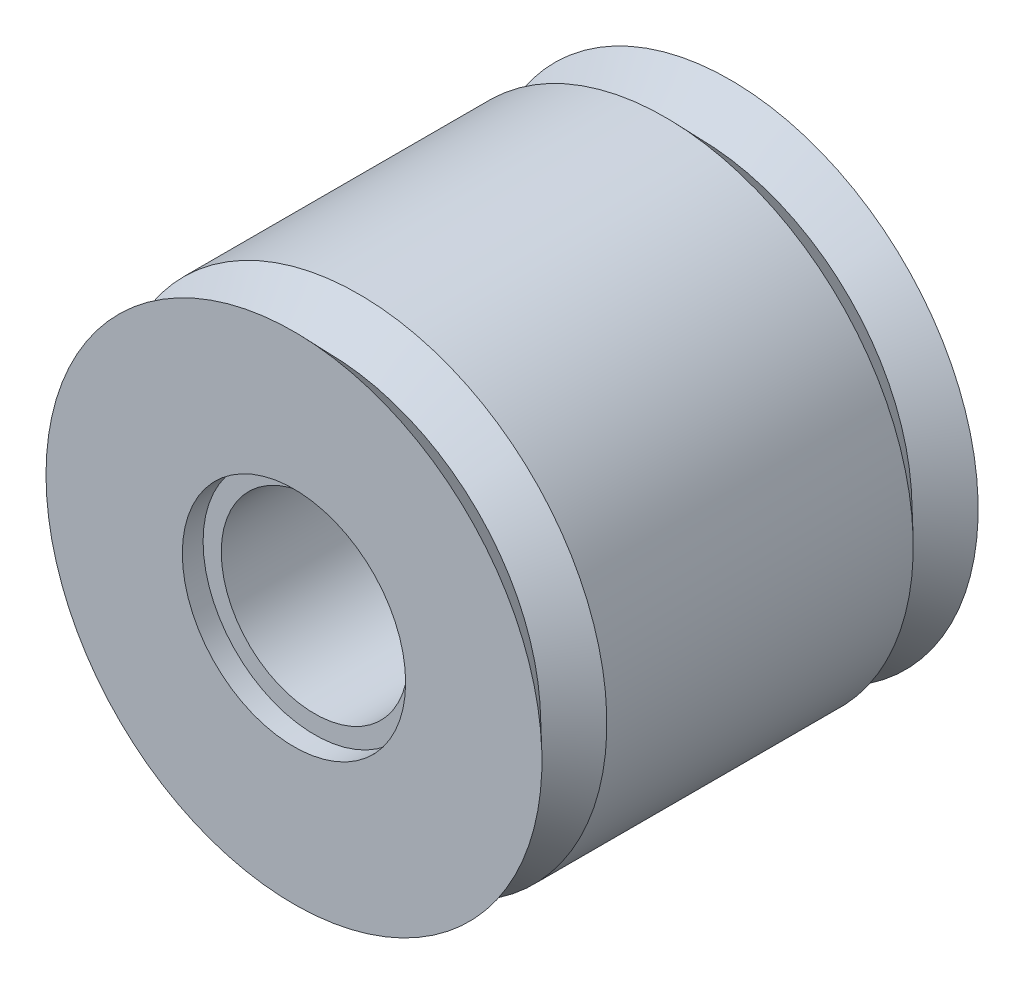
SolidWorks part; units mm, degrees
ref_plane "정면" through (0, 0, 0) normal (0, 0, 1) x (1, 0, 0)
ref_plane "윗면" through (0, 0, 0) normal (0, 1, 0) x (1, 0, 0)
ref_plane "우측면" through (0, 0, 0) normal (1, 0, 0) x (0, 0, -1)
sketch "스케치1" plane through (0, 0, 0) normal (0, 0, 1) x (1, 0, 0)
  circle A0 centre (0, 0) radius 9.55
  circle A1 centre (0, 0) radius 3.6
  dimension "D1" = 19.1
  dimension "D2" = 7.2
extrude "보스-돌출1" add sketch "스케치1" along normal mid plane 16.8
sketch "스케치2" plane through (0, 0, 8.4) normal (0, 0, 1) x (1, 0, 0)
  circle A0 centre (0, 0) radius 4.3
  dimension "D1" = 8.6
extrude "컷-돌출1" cut sketch "스케치2" against normal blind 0.8
sketch "스케치3" plane through (0, 0, 0) normal (1, 0, 0) x (0, 0, -1)
  line L0 (-8.4, 9.55) -> (-5.9, 9.55)
  line L1 (8.4, 9.55) -> (-8.4, 9.55) construction
  line L2 (-5.9, 9.55) -> (-7.15, 8.25)
  line L3 (-7.15, 8.25) -> (-8.4, 9.55)
  line L4 (0, 0) -> (-8.4, 0) construction
  line L5 (-8.4, 9.55) -> (-8.4, -9.55) construction
  line L6 (-7.15, 8.25) -> (-7.15, 9.55) construction
  dimension "D1" = 2.5
  dimension "D2" = 1.3
revolve "컷-회전1" cut sketch "스케치3" angle 360 about L4
mirror "대칭 복사1" about plane through (0, 0, 0) normal (0, 0, 1) of "컷-회전1", "컷-돌출1"
